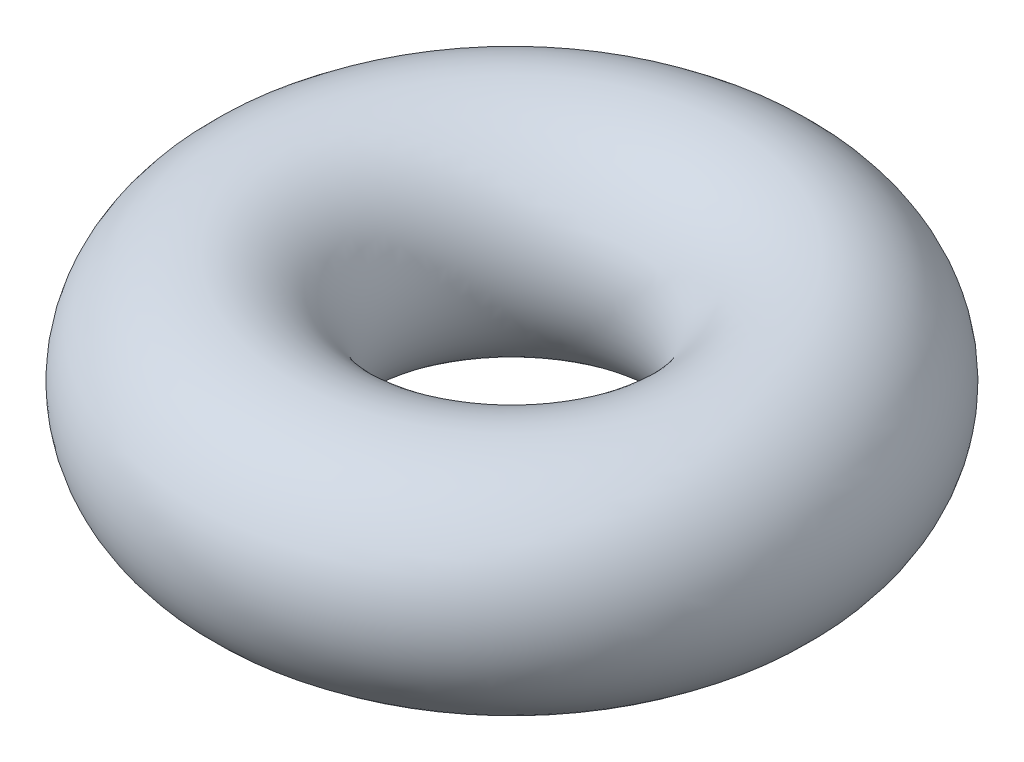
SolidWorks part; units mm, degrees
ref_plane "Front Plane" through (0, 0, 0) normal (0, 0, 1) x (1, 0, 0)
ref_plane "Top Plane" through (0, 0, 0) normal (0, 1, 0) x (1, 0, 0)
ref_plane "Right Plane" through (0, 0, 0) normal (1, 0, 0) x (0, 0, -1)
sketch "Sketch2" plane through (0, 0, 0) normal (0, 0, 1) x (1, 0, 0)
  line L0 (0, 0) -> (-121, 0) construction
  line L1 (0, 0) -> (0, 46.1456) construction
  circle A0 centre (-121, 0) radius 60.5
  dimension "D2" = 121
  dimension "D1" = 121
ref_axis "Axis1" through (0, 0, 0) along (0, 1, 0)
revolve "Revolve2" add sketch "Sketch2" angle 360 about axis through (0, 0, 0) along (0, 1, 0)
ref_plane "Plane1" through (0, 0, 0) normal (0, 1, 0) x (1, 0, 0)
